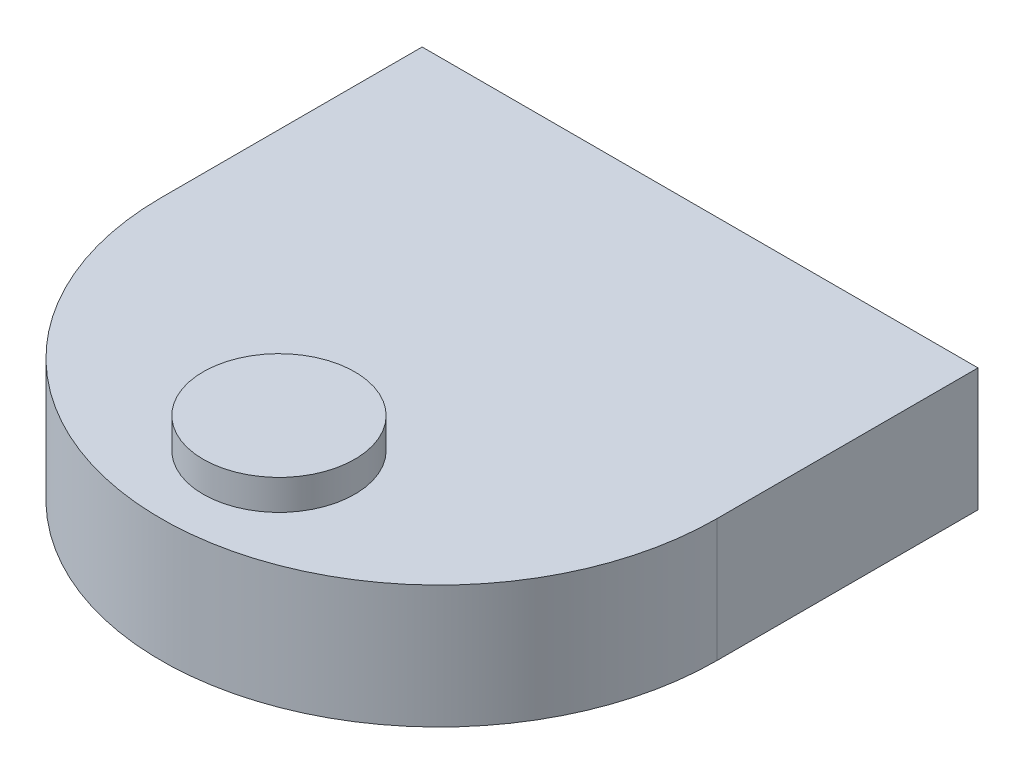
SolidWorks part; units mm, degrees
ref_plane "Front Plane" through (0, 0, 0) normal (0, 0, 1) x (1, 0, 0)
ref_plane "Top Plane" through (0, 0, 0) normal (0, 1, 0) x (1, 0, 0)
ref_plane "Right Plane" through (0, 0, 0) normal (1, 0, 0) x (0, 0, -1)
sketch "Sketch1" plane through (0, 0, 0) normal (0, 1, 0) x (1, 0, 0)
  line L0 (-165, 0) -> (-165, 155)
  line L1 (-165, 155) -> (165, 155)
  line L2 (165, 155) -> (165, 0)
  circle A0 centre (0, 0) radius 165
  point P5 (0, -165)
  dimension "D1" = 330
  dimension "D2" = 320
extrude "Boss-Extrude1" add sketch "Sketch1" along normal blind 73 contours A0 L1 | A0 L1 L0 | A0 L2 L1
sketch "Sketch2" plane through (0, 73, 0) normal (0, 1, 0) x (1, 0, 0)
  circle A0 centre (0, -95) radius 45
  arc A1 (-165, 0) -> (165, 0) centre (0, 0) ccw construction
  point P2 (0, -165)
  dimension "D2" = 90
  dimension "D1" = 70
extrude "Boss-Extrude2" add sketch "Sketch2" along normal blind 18
sketch "Sketch3" plane through (0, 0, 0) normal (0, -1, 0) x (1, 0, 0)
  line L1 (-127.5, -40) -> (-107.5, -40)
  line L2 (-127.5, -40) -> (-127.5, 40)
  line L3 (-127.5, 40) -> (-107.5, 40)
  line L4 (-107.5, -40) -> (-107.5, 40)
  line L5 (-127.5, -40) -> (-107.5, 40) construction
  line L6 (-127.5, 40) -> (-107.5, -40) construction
  line L7 (107.5, -40) -> (127.5, -40)
  line L8 (107.5, -40) -> (107.5, 40)
  line L9 (107.5, 40) -> (127.5, 40)
  line L10 (127.5, -40) -> (127.5, 40)
  line L11 (107.5, -40) -> (127.5, 40) construction
  line L12 (107.5, 40) -> (127.5, -40) construction
  point P0 (-117.5, 0)
  point P5 (117.5, 0)
  dimension "D1" = 80
  dimension "D2" = 20
  dimension "D3" = 117.5
  dimension "D4" = 117.5
sketch "Sketch4" plane through (0, 0, 0) normal (0, -1, 0) x (1, 0, 0)
  line L0 (-100, 100) -> (-80, 100)
  circle A0 centre (-90, 100) radius 10
  dimension "D3" = 20
  dimension "D1" = 100
  dimension "D2" = 90
revolve "Revolve1" add sketch "Sketch4" angle 360 about L0
extrude "Cut-Extrude2" cut sketch "Sketch3" against normal blind 27.5
sketch "Sketch5" plane through (0, 27.5, 0) normal (0, -1, 0) x (1, 0, 0)
  line L0 (-127.5, 0) -> (-107.5, 0)
  line L1 (-127.5, -40) -> (-107.5, -40)
  line L2 (-127.5, -40) -> (-127.5, 40)
  line L3 (-127.5, 40) -> (-107.5, 40)
  line L4 (-107.5, -40) -> (-107.5, 40)
  line L5 (-127.5, -40) -> (-107.5, 40) construction
  line L6 (-127.5, 40) -> (-107.5, -40) construction
  line L7 (107.5, 0) -> (127.5, 0)
  line L8 (107.5, -40) -> (127.5, -40)
  line L9 (107.5, -40) -> (107.5, 40)
  line L10 (107.5, 40) -> (127.5, 40)
  line L11 (127.5, -40) -> (127.5, 40)
  line L12 (107.5, -40) -> (127.5, 40) construction
  line L13 (107.5, 40) -> (127.5, -40) construction
  point P0 (-117.5, 0)
  point P8 (117.5, 0)
  dimension "D1" = 20
  dimension "D2" = 80
  dimension "D3" = 80
  dimension "D4" = 20
revolve "Cut-Revolve2" cut sketch "Sketch5" angle 360 about L0
pattern_linear "LPattern2" count 2 spacing 180 along (1, 0, 0) count 2 spacing 200 along (0, 0, -1) of "Revolve1"
